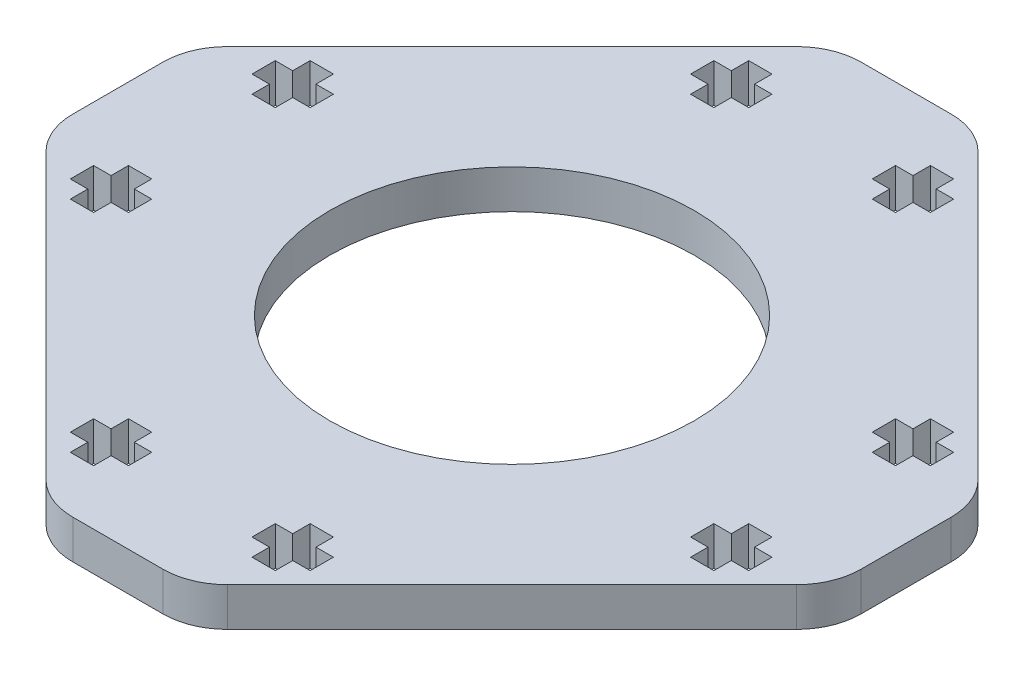
SolidWorks part; units mm, degrees
ref_plane "Front Plane" through (0, 0, 0) normal (0, 0, 1) x (1, 0, 0)
ref_plane "Top Plane" through (0, 0, 0) normal (0, 1, 0) x (1, 0, 0)
ref_plane "Right Plane" through (0, 0, 0) normal (1, 0, 0) x (0, 0, -1)
sketch "Sketch1" plane through (0, 0, 0) normal (0, 1, 0) x (1, 0, 0)
  line L0 (3.4914, 30.5) -> (-3.4914, 30.5)
  line L1 (-7.0269, 29.0355) -> (-29.0355, 7.0269)
  line L2 (-30.5, 3.4914) -> (-30.5, -3.4914)
  line L3 (-29.0355, -7.0269) -> (-7.0269, -29.0355)
  line L4 (-3.4914, -30.5) -> (3.4914, -30.5)
  line L5 (7.0269, -29.0355) -> (29.0355, -7.0269)
  line L7 (29.0355, 7.0269) -> (7.0269, 29.0355)
  line L13 (30.5, -3.4914) -> (30.5, 3.4914) construction
  line L14 (30.5, -3.4914) -> (30.5, 3.4914)
  arc A0 (7.0269, 29.0355) -> (3.4914, 30.5) centre (3.4914, 25.5) ccw
  arc A1 (-3.4914, 30.5) -> (-7.0269, 29.0355) centre (-3.4914, 25.5) ccw
  arc A2 (-29.0355, 7.0269) -> (-30.5, 3.4914) centre (-25.5, 3.4914) ccw
  arc A3 (-30.5, -3.4914) -> (-29.0355, -7.0269) centre (-25.5, -3.4914) ccw
  arc A4 (-7.0269, -29.0355) -> (-3.4914, -30.5) centre (-3.4914, -25.5) ccw
  arc A5 (3.4914, -30.5) -> (7.0269, -29.0355) centre (3.4914, -25.5) ccw
  circle A16 centre (0, 0) radius 14.1
  arc A17 (29.0355, -7.0269) -> (30.5, -3.4914) centre (25.5, -3.4914) ccw construction
  arc A18 (30.5, 3.4914) -> (29.0355, 7.0269) centre (25.5, 3.4914) ccw construction
  arc A19 (29.0355, -7.0269) -> (30.5, -3.4914) centre (25.5, -3.4914) ccw
  arc A20 (30.5, 3.4914) -> (29.0355, 7.0269) centre (25.5, 3.4914) ccw
  dimension "D1" = 28.2
  dimension "D2" = 31.1249
  dimension "D3" = 51
extrude "Boss-Extrude1" add sketch "Sketch1" along normal blind 3
sketch "Sketch2" plane through (0, 3, 0) normal (0, 1, 0) x (1, 0, 0)
  line L12 (-26.25, 7.9294) -> (-26.25, 6.1294)
  line L13 (-26.25, 6.1294) -> (-24.9, 6.1294)
  line L14 (-24.9, 6.1294) -> (-24.9, 4.7794)
  line L15 (-24.9, 4.7794) -> (-23.1, 4.7794)
  line L16 (-23.1, 4.7794) -> (-23.1, 6.1294)
  line L17 (-23.1, 6.1294) -> (-21.75, 6.1294)
  line L18 (-21.75, 6.1294) -> (-21.75, 7.9294)
  line L19 (-21.75, 7.9294) -> (-23.1, 7.9294)
  line L20 (-23.1, 7.9294) -> (-23.1, 9.2794)
  line L21 (-23.1, 9.2794) -> (-24.9, 9.2794)
  line L22 (-24.9, 9.2794) -> (-24.9, 7.9294)
  line L23 (-24.9, 7.9294) -> (-26.25, 7.9294)
  line L24 (-26.25, 7.9294) -> (-26.25, 6.1294)
  line L25 (-26.25, 6.1294) -> (-24.9, 6.1294)
  line L26 (-24.9, 6.1294) -> (-24.9, 4.7794)
  line L27 (-24.9, 4.7794) -> (-23.1, 4.7794)
  line L28 (-23.1, 4.7794) -> (-23.1, 6.1294)
  line L29 (-23.1, 6.1294) -> (-21.75, 6.1294)
  line L30 (-21.75, 6.1294) -> (-21.75, 7.9294)
  line L31 (-21.75, 7.9294) -> (-23.1, 7.9294)
  line L32 (-23.1, 7.9294) -> (-23.1, 9.2794)
  line L33 (-23.1, 9.2794) -> (-24.9, 9.2794)
  line L34 (-24.9, 9.2794) -> (-24.9, 7.9294)
  line L35 (-24.9, 7.9294) -> (-26.25, 7.9294)
  line L36 (-23.1, -4.7794) -> (-24.9, -4.7794)
  line L37 (-24.9, -4.7794) -> (-24.9, -6.1294)
  line L38 (-24.9, -6.1294) -> (-26.25, -6.1294)
  line L39 (-26.25, -6.1294) -> (-26.25, -7.9294)
  line L40 (-26.25, -7.9294) -> (-24.9, -7.9294)
  line L41 (-24.9, -7.9294) -> (-24.9, -9.2794)
  line L42 (-24.9, -9.2794) -> (-23.1, -9.2794)
  line L43 (-23.1, -9.2794) -> (-23.1, -7.9294)
  line L44 (-23.1, -7.9294) -> (-21.75, -7.9294)
  line L45 (-21.75, -7.9294) -> (-21.75, -6.1294)
  line L46 (-21.75, -6.1294) -> (-23.1, -6.1294)
  line L47 (-23.1, -6.1294) -> (-23.1, -4.7794)
  line L48 (-23.1, -4.7794) -> (-24.9, -4.7794)
  line L49 (-24.9, -4.7794) -> (-24.9, -6.1294)
  line L50 (-24.9, -6.1294) -> (-26.25, -6.1294)
  line L51 (-26.25, -6.1294) -> (-26.25, -7.9294)
  line L52 (-26.25, -7.9294) -> (-24.9, -7.9294)
  line L53 (-24.9, -7.9294) -> (-24.9, -9.2794)
  line L54 (-24.9, -9.2794) -> (-23.1, -9.2794)
  line L55 (-23.1, -9.2794) -> (-23.1, -7.9294)
  line L56 (-23.1, -7.9294) -> (-21.75, -7.9294)
  line L57 (-21.75, -7.9294) -> (-21.75, -6.1294)
  line L58 (-21.75, -6.1294) -> (-23.1, -6.1294)
  line L59 (-23.1, -6.1294) -> (-23.1, -4.7794)
  line L60 (7.9294, 23.1) -> (9.2794, 23.1)
  line L61 (9.2794, 23.1) -> (9.2794, 24.9)
  line L62 (9.2794, 24.9) -> (7.9294, 24.9)
  line L63 (7.9294, 24.9) -> (7.9294, 26.25)
  line L64 (7.9294, 26.25) -> (6.1294, 26.25)
  line L65 (6.1294, 26.25) -> (6.1294, 24.9)
  line L66 (6.1294, 24.9) -> (4.7794, 24.9)
  line L67 (4.7794, 24.9) -> (4.7794, 23.1)
  line L68 (4.7794, 23.1) -> (6.1294, 23.1)
  line L69 (6.1294, 23.1) -> (6.1294, 21.75)
  line L70 (6.1294, 21.75) -> (7.9294, 21.75)
  line L71 (7.9294, 21.75) -> (7.9294, 23.1)
  line L72 (7.9294, 23.1) -> (9.2794, 23.1)
  line L73 (9.2794, 23.1) -> (9.2794, 24.9)
  line L74 (9.2794, 24.9) -> (7.9294, 24.9)
  line L75 (7.9294, 24.9) -> (7.9294, 26.25)
  line L76 (7.9294, 26.25) -> (6.1294, 26.25)
  line L77 (6.1294, 26.25) -> (6.1294, 24.9)
  line L78 (6.1294, 24.9) -> (4.7794, 24.9)
  line L79 (4.7794, 24.9) -> (4.7794, 23.1)
  line L80 (4.7794, 23.1) -> (6.1294, 23.1)
  line L81 (6.1294, 23.1) -> (6.1294, 21.75)
  line L82 (6.1294, 21.75) -> (7.9294, 21.75)
  line L83 (7.9294, 21.75) -> (7.9294, 23.1)
  line L84 (26.25, -7.9294) -> (26.25, -6.1294)
  line L85 (26.25, -6.1294) -> (24.9, -6.1294)
  line L86 (24.9, -6.1294) -> (24.9, -4.7794)
  line L87 (24.9, -4.7794) -> (23.1, -4.7794)
  line L88 (23.1, -4.7794) -> (23.1, -6.1294)
  line L89 (23.1, -6.1294) -> (21.75, -6.1294)
  line L90 (21.75, -6.1294) -> (21.75, -7.9294)
  line L91 (21.75, -7.9294) -> (23.1, -7.9294)
  line L92 (23.1, -7.9294) -> (23.1, -9.2794)
  line L93 (23.1, -9.2794) -> (24.9, -9.2794)
  line L94 (24.9, -9.2794) -> (24.9, -7.9294)
  line L95 (24.9, -7.9294) -> (26.25, -7.9294)
  line L96 (26.25, -7.9294) -> (26.25, -6.1294)
  line L97 (26.25, -6.1294) -> (24.9, -6.1294)
  line L98 (24.9, -6.1294) -> (24.9, -4.7794)
  line L99 (24.9, -4.7794) -> (23.1, -4.7794)
  line L100 (23.1, -4.7794) -> (23.1, -6.1294)
  line L101 (23.1, -6.1294) -> (21.75, -6.1294)
  line L102 (21.75, -6.1294) -> (21.75, -7.9294)
  line L103 (21.75, -7.9294) -> (23.1, -7.9294)
  line L104 (23.1, -7.9294) -> (23.1, -9.2794)
  line L105 (23.1, -9.2794) -> (24.9, -9.2794)
  line L106 (24.9, -9.2794) -> (24.9, -7.9294)
  line L107 (24.9, -7.9294) -> (26.25, -7.9294)
  line L108 (-4.7794, 24.9) -> (-6.1294, 24.9)
  line L109 (-6.1294, 24.9) -> (-6.1294, 26.25)
  line L110 (-6.1294, 26.25) -> (-7.9294, 26.25)
  line L111 (-7.9294, 26.25) -> (-7.9294, 24.9)
  line L112 (-7.9294, 24.9) -> (-9.2794, 24.9)
  line L113 (-9.2794, 24.9) -> (-9.2794, 23.1)
  line L114 (-9.2794, 23.1) -> (-7.9294, 23.1)
  line L115 (-7.9294, 23.1) -> (-7.9294, 21.75)
  line L116 (-7.9294, 21.75) -> (-6.1294, 21.75)
  line L117 (-6.1294, 21.75) -> (-6.1294, 23.1)
  line L118 (-6.1294, 23.1) -> (-4.7794, 23.1)
  line L119 (-4.7794, 23.1) -> (-4.7794, 24.9)
  line L120 (-4.7794, 24.9) -> (-6.1294, 24.9)
  line L121 (-6.1294, 24.9) -> (-6.1294, 26.25)
  line L122 (-6.1294, 26.25) -> (-7.9294, 26.25)
  line L123 (-7.9294, 26.25) -> (-7.9294, 24.9)
  line L124 (-7.9294, 24.9) -> (-9.2794, 24.9)
  line L125 (-9.2794, 24.9) -> (-9.2794, 23.1)
  line L126 (-9.2794, 23.1) -> (-7.9294, 23.1)
  line L127 (-7.9294, 23.1) -> (-7.9294, 21.75)
  line L128 (-7.9294, 21.75) -> (-6.1294, 21.75)
  line L129 (-6.1294, 21.75) -> (-6.1294, 23.1)
  line L130 (-6.1294, 23.1) -> (-4.7794, 23.1)
  line L131 (-4.7794, 23.1) -> (-4.7794, 24.9)
  line L132 (26.25, 7.9294) -> (24.9, 7.9294)
  line L133 (26.25, 6.1294) -> (26.25, 7.9294)
  line L134 (24.9, 6.1294) -> (26.25, 6.1294)
  line L135 (24.9, 4.7794) -> (24.9, 6.1294)
  line L136 (23.1, 4.7794) -> (24.9, 4.7794)
  line L137 (23.1, 6.1294) -> (23.1, 4.7794)
  line L138 (21.75, 6.1294) -> (23.1, 6.1294)
  line L139 (21.75, 7.9294) -> (21.75, 6.1294)
  line L140 (23.1, 7.9294) -> (21.75, 7.9294)
  line L141 (23.1, 9.2794) -> (23.1, 7.9294)
  line L142 (24.9, 9.2794) -> (23.1, 9.2794)
  line L143 (24.9, 7.9294) -> (24.9, 9.2794)
  line L144 (26.25, 7.9294) -> (24.9, 7.9294)
  line L145 (26.25, 6.1294) -> (26.25, 7.9294)
  line L146 (24.9, 6.1294) -> (26.25, 6.1294)
  line L147 (24.9, 4.7794) -> (24.9, 6.1294)
  line L148 (23.1, 4.7794) -> (24.9, 4.7794)
  line L149 (23.1, 6.1294) -> (23.1, 4.7794)
  line L150 (21.75, 6.1294) -> (23.1, 6.1294)
  line L151 (21.75, 7.9294) -> (21.75, 6.1294)
  line L152 (23.1, 7.9294) -> (21.75, 7.9294)
  line L153 (23.1, 9.2794) -> (23.1, 7.9294)
  line L154 (24.9, 9.2794) -> (23.1, 9.2794)
  line L155 (24.9, 7.9294) -> (24.9, 9.2794)
  line L156 (-6.1294, -26.25) -> (-6.1294, -24.9)
  line L157 (-6.1294, -24.9) -> (-4.7794, -24.9)
  line L158 (-4.7794, -24.9) -> (-4.7794, -23.1)
  line L159 (-4.7794, -23.1) -> (-6.1294, -23.1)
  line L160 (-6.1294, -23.1) -> (-6.1294, -21.75)
  line L161 (-6.1294, -21.75) -> (-7.9294, -21.75)
  line L162 (-7.9294, -21.75) -> (-7.9294, -23.1)
  line L163 (-7.9294, -23.1) -> (-9.2794, -23.1)
  line L164 (-9.2794, -23.1) -> (-9.2794, -24.9)
  line L165 (-9.2794, -24.9) -> (-7.9294, -24.9)
  line L166 (-7.9294, -24.9) -> (-7.9294, -26.25)
  line L167 (-7.9294, -26.25) -> (-6.1294, -26.25)
  line L168 (-6.1294, -26.25) -> (-6.1294, -24.9)
  line L169 (-6.1294, -24.9) -> (-4.7794, -24.9)
  line L170 (-4.7794, -24.9) -> (-4.7794, -23.1)
  line L171 (-4.7794, -23.1) -> (-6.1294, -23.1)
  line L172 (-6.1294, -23.1) -> (-6.1294, -21.75)
  line L173 (-6.1294, -21.75) -> (-7.9294, -21.75)
  line L174 (-7.9294, -21.75) -> (-7.9294, -23.1)
  line L175 (-7.9294, -23.1) -> (-9.2794, -23.1)
  line L176 (-9.2794, -23.1) -> (-9.2794, -24.9)
  line L177 (-9.2794, -24.9) -> (-7.9294, -24.9)
  line L178 (-7.9294, -24.9) -> (-7.9294, -26.25)
  line L179 (-7.9294, -26.25) -> (-6.1294, -26.25)
  line L180 (7.9294, -26.25) -> (7.9294, -24.9)
  line L181 (7.9294, -24.9) -> (9.2794, -24.9)
  line L182 (9.2794, -24.9) -> (9.2794, -23.1)
  line L183 (9.2794, -23.1) -> (7.9294, -23.1)
  line L184 (7.9294, -23.1) -> (7.9294, -21.75)
  line L185 (7.9294, -21.75) -> (6.1294, -21.75)
  line L186 (6.1294, -21.75) -> (6.1294, -23.1)
  line L187 (6.1294, -23.1) -> (4.7794, -23.1)
  line L188 (4.7794, -23.1) -> (4.7794, -24.9)
  line L189 (4.7794, -24.9) -> (6.1294, -24.9)
  line L190 (6.1294, -24.9) -> (6.1294, -26.25)
  line L191 (6.1294, -26.25) -> (7.9294, -26.25)
  line L192 (7.9294, -26.25) -> (7.9294, -24.9)
  line L193 (7.9294, -24.9) -> (9.2794, -24.9)
  line L194 (9.2794, -24.9) -> (9.2794, -23.1)
  line L195 (9.2794, -23.1) -> (7.9294, -23.1)
  line L196 (7.9294, -23.1) -> (7.9294, -21.75)
  line L197 (7.9294, -21.75) -> (6.1294, -21.75)
  line L198 (6.1294, -21.75) -> (6.1294, -23.1)
  line L199 (6.1294, -23.1) -> (4.7794, -23.1)
  line L200 (4.7794, -23.1) -> (4.7794, -24.9)
  line L201 (4.7794, -24.9) -> (6.1294, -24.9)
  line L202 (6.1294, -24.9) -> (6.1294, -26.25)
  line L203 (6.1294, -26.25) -> (7.9294, -26.25)
  dimension "D1" = 0
  dimension "D2" = 0
  dimension "D3" = 0
  dimension "D4" = 0
  dimension "D5" = 0
  dimension "D6" = 0
  dimension "D7" = 0
  dimension "D8" = 0
extrude "Cut-Extrude1" cut sketch "Sketch2" against normal through all
sketch "Sketch3" plane through (0, 3, 0) normal (0, 1, 0) x (1, 0, 0)
  line L8 (3.4914, 30.5) -> (-3.4914, 30.5)
  line L9 (-7.0269, 29.0355) -> (-29.0355, 7.0269)
  line L10 (-30.5, 3.4914) -> (-30.5, -3.4914)
  line L11 (-29.0355, -7.0269) -> (-7.0269, -29.0355)
  line L12 (-3.4914, -30.5) -> (3.4914, -30.5)
  line L13 (7.0269, -29.0355) -> (29.0355, -7.0269)
  line L14 (30.5, -3.4914) -> (30.5, 3.4914)
  line L15 (29.0355, 7.0269) -> (7.0269, 29.0355)
  line L16 (3.4914, 30.5) -> (-3.4914, 30.5)
  line L17 (-7.0269, 29.0355) -> (-29.0355, 7.0269)
  line L18 (-30.5, 3.4914) -> (-30.5, -3.4914)
  line L19 (-29.0355, -7.0269) -> (-7.0269, -29.0355)
  line L20 (-3.4914, -30.5) -> (3.4914, -30.5)
  line L21 (7.0269, -29.0355) -> (29.0355, -7.0269)
  line L22 (30.5, -3.4914) -> (30.5, 3.4914)
  line L23 (29.0355, 7.0269) -> (7.0269, 29.0355)
  line L28 (-24.9, 7.9294) -> (-26.25, 7.9294)
  line L29 (-24.9, 9.2794) -> (-24.9, 7.9294)
  line L30 (-23.1, 9.2794) -> (-24.9, 9.2794)
  line L31 (-23.1, 7.9294) -> (-23.1, 9.2794)
  line L32 (-21.75, 7.9294) -> (-23.1, 7.9294)
  line L33 (-21.75, 6.1294) -> (-21.75, 7.9294)
  line L34 (-23.1, 6.1294) -> (-21.75, 6.1294)
  line L35 (-23.1, 4.7794) -> (-23.1, 6.1294)
  line L36 (-24.9, 4.7794) -> (-23.1, 4.7794)
  line L37 (-24.9, 6.1294) -> (-24.9, 4.7794)
  line L38 (-26.25, 6.1294) -> (-24.9, 6.1294)
  line L39 (-26.25, 7.9294) -> (-26.25, 6.1294)
  line L40 (-24.9, 7.9294) -> (-26.25, 7.9294)
  line L41 (-24.9, 9.2794) -> (-24.9, 7.9294)
  line L42 (-23.1, 9.2794) -> (-24.9, 9.2794)
  line L43 (-23.1, 7.9294) -> (-23.1, 9.2794)
  line L44 (-21.75, 7.9294) -> (-23.1, 7.9294)
  line L45 (-21.75, 6.1294) -> (-21.75, 7.9294)
  line L46 (-23.1, 6.1294) -> (-21.75, 6.1294)
  line L47 (-23.1, 4.7794) -> (-23.1, 6.1294)
  line L48 (-24.9, 4.7794) -> (-23.1, 4.7794)
  line L49 (-24.9, 6.1294) -> (-24.9, 4.7794)
  line L50 (-26.25, 6.1294) -> (-24.9, 6.1294)
  line L51 (-26.25, 7.9294) -> (-26.25, 6.1294)
  line L52 (24.9, 7.9294) -> (24.9, 9.2794)
  line L53 (26.25, 7.9294) -> (24.9, 7.9294)
  line L54 (26.25, 6.1294) -> (26.25, 7.9294)
  line L55 (24.9, 6.1294) -> (26.25, 6.1294)
  line L56 (24.9, 4.7794) -> (24.9, 6.1294)
  line L57 (23.1, 4.7794) -> (24.9, 4.7794)
  line L58 (23.1, 6.1294) -> (23.1, 4.7794)
  line L59 (21.75, 6.1294) -> (23.1, 6.1294)
  line L60 (21.75, 7.9294) -> (21.75, 6.1294)
  line L61 (23.1, 7.9294) -> (21.75, 7.9294)
  line L62 (23.1, 9.2794) -> (23.1, 7.9294)
  line L63 (24.9, 9.2794) -> (23.1, 9.2794)
  line L64 (24.9, 7.9294) -> (24.9, 9.2794)
  line L65 (26.25, 7.9294) -> (24.9, 7.9294)
  line L66 (26.25, 6.1294) -> (26.25, 7.9294)
  line L67 (24.9, 6.1294) -> (26.25, 6.1294)
  line L68 (24.9, 4.7794) -> (24.9, 6.1294)
  line L69 (23.1, 4.7794) -> (24.9, 4.7794)
  line L70 (23.1, 6.1294) -> (23.1, 4.7794)
  line L71 (21.75, 6.1294) -> (23.1, 6.1294)
  line L72 (21.75, 7.9294) -> (21.75, 6.1294)
  line L73 (23.1, 7.9294) -> (21.75, 7.9294)
  line L74 (23.1, 9.2794) -> (23.1, 7.9294)
  line L75 (24.9, 9.2794) -> (23.1, 9.2794)
  line L76 (-7.9294, -26.25) -> (-6.1294, -26.25)
  line L77 (-7.9294, -24.9) -> (-7.9294, -26.25)
  line L78 (-9.2794, -24.9) -> (-7.9294, -24.9)
  line L79 (-9.2794, -23.1) -> (-9.2794, -24.9)
  line L80 (-7.9294, -23.1) -> (-9.2794, -23.1)
  line L81 (-7.9294, -21.75) -> (-7.9294, -23.1)
  line L82 (-6.1294, -21.75) -> (-7.9294, -21.75)
  line L83 (-6.1294, -23.1) -> (-6.1294, -21.75)
  line L84 (-4.7794, -23.1) -> (-6.1294, -23.1)
  line L85 (-4.7794, -24.9) -> (-4.7794, -23.1)
  line L86 (-6.1294, -24.9) -> (-4.7794, -24.9)
  line L87 (-6.1294, -26.25) -> (-6.1294, -24.9)
  line L88 (-7.9294, -26.25) -> (-6.1294, -26.25)
  line L89 (-7.9294, -24.9) -> (-7.9294, -26.25)
  line L90 (-9.2794, -24.9) -> (-7.9294, -24.9)
  line L91 (-9.2794, -23.1) -> (-9.2794, -24.9)
  line L92 (-7.9294, -23.1) -> (-9.2794, -23.1)
  line L93 (-7.9294, -21.75) -> (-7.9294, -23.1)
  line L94 (-6.1294, -21.75) -> (-7.9294, -21.75)
  line L95 (-6.1294, -23.1) -> (-6.1294, -21.75)
  line L96 (-4.7794, -23.1) -> (-6.1294, -23.1)
  line L97 (-4.7794, -24.9) -> (-4.7794, -23.1)
  line L98 (-6.1294, -24.9) -> (-4.7794, -24.9)
  line L99 (-6.1294, -26.25) -> (-6.1294, -24.9)
  line L100 (7.9294, -24.9) -> (9.2794, -24.9)
  line L101 (7.9294, -26.25) -> (7.9294, -24.9)
  line L102 (6.1294, -26.25) -> (7.9294, -26.25)
  line L103 (6.1294, -24.9) -> (6.1294, -26.25)
  line L104 (4.7794, -24.9) -> (6.1294, -24.9)
  line L105 (4.7794, -23.1) -> (4.7794, -24.9)
  line L106 (6.1294, -23.1) -> (4.7794, -23.1)
  line L107 (6.1294, -21.75) -> (6.1294, -23.1)
  line L108 (7.9294, -21.75) -> (6.1294, -21.75)
  line L109 (7.9294, -23.1) -> (7.9294, -21.75)
  line L110 (9.2794, -23.1) -> (7.9294, -23.1)
  line L111 (9.2794, -24.9) -> (9.2794, -23.1)
  line L112 (7.9294, -24.9) -> (9.2794, -24.9)
  line L113 (7.9294, -26.25) -> (7.9294, -24.9)
  line L114 (6.1294, -26.25) -> (7.9294, -26.25)
  line L115 (6.1294, -24.9) -> (6.1294, -26.25)
  line L116 (4.7794, -24.9) -> (6.1294, -24.9)
  line L117 (4.7794, -23.1) -> (4.7794, -24.9)
  line L118 (6.1294, -23.1) -> (4.7794, -23.1)
  line L119 (6.1294, -21.75) -> (6.1294, -23.1)
  line L120 (7.9294, -21.75) -> (6.1294, -21.75)
  line L121 (7.9294, -23.1) -> (7.9294, -21.75)
  line L122 (9.2794, -23.1) -> (7.9294, -23.1)
  line L123 (9.2794, -24.9) -> (9.2794, -23.1)
  line L124 (-24.9, -4.7794) -> (-24.9, -6.1294)
  line L125 (-23.1, -4.7794) -> (-24.9, -4.7794)
  line L126 (-23.1, -6.1294) -> (-23.1, -4.7794)
  line L127 (-21.75, -6.1294) -> (-23.1, -6.1294)
  line L128 (-21.75, -7.9294) -> (-21.75, -6.1294)
  line L129 (-23.1, -7.9294) -> (-21.75, -7.9294)
  line L130 (-23.1, -9.2794) -> (-23.1, -7.9294)
  line L131 (-24.9, -9.2794) -> (-23.1, -9.2794)
  line L132 (-24.9, -7.9294) -> (-24.9, -9.2794)
  line L133 (-26.25, -7.9294) -> (-24.9, -7.9294)
  line L134 (-26.25, -6.1294) -> (-26.25, -7.9294)
  line L135 (-24.9, -6.1294) -> (-26.25, -6.1294)
  line L136 (-24.9, -4.7794) -> (-24.9, -6.1294)
  line L137 (-23.1, -4.7794) -> (-24.9, -4.7794)
  line L138 (-23.1, -6.1294) -> (-23.1, -4.7794)
  line L139 (-21.75, -6.1294) -> (-23.1, -6.1294)
  line L140 (-21.75, -7.9294) -> (-21.75, -6.1294)
  line L141 (-23.1, -7.9294) -> (-21.75, -7.9294)
  line L142 (-23.1, -9.2794) -> (-23.1, -7.9294)
  line L143 (-24.9, -9.2794) -> (-23.1, -9.2794)
  line L144 (-24.9, -7.9294) -> (-24.9, -9.2794)
  line L145 (-26.25, -7.9294) -> (-24.9, -7.9294)
  line L146 (-26.25, -6.1294) -> (-26.25, -7.9294)
  line L147 (-24.9, -6.1294) -> (-26.25, -6.1294)
  line L148 (7.9294, 21.75) -> (7.9294, 23.1)
  line L149 (6.1294, 21.75) -> (7.9294, 21.75)
  line L150 (6.1294, 23.1) -> (6.1294, 21.75)
  line L151 (4.7794, 23.1) -> (6.1294, 23.1)
  line L152 (4.7794, 24.9) -> (4.7794, 23.1)
  line L153 (6.1294, 24.9) -> (4.7794, 24.9)
  line L154 (6.1294, 26.25) -> (6.1294, 24.9)
  line L155 (7.9294, 26.25) -> (6.1294, 26.25)
  line L156 (7.9294, 24.9) -> (7.9294, 26.25)
  line L157 (9.2794, 24.9) -> (7.9294, 24.9)
  line L158 (9.2794, 23.1) -> (9.2794, 24.9)
  line L159 (7.9294, 23.1) -> (9.2794, 23.1)
  line L160 (7.9294, 21.75) -> (7.9294, 23.1)
  line L161 (6.1294, 21.75) -> (7.9294, 21.75)
  line L162 (6.1294, 23.1) -> (6.1294, 21.75)
  line L163 (4.7794, 23.1) -> (6.1294, 23.1)
  line L164 (4.7794, 24.9) -> (4.7794, 23.1)
  line L165 (6.1294, 24.9) -> (4.7794, 24.9)
  line L166 (6.1294, 26.25) -> (6.1294, 24.9)
  line L167 (7.9294, 26.25) -> (6.1294, 26.25)
  line L168 (7.9294, 24.9) -> (7.9294, 26.25)
  line L169 (9.2794, 24.9) -> (7.9294, 24.9)
  line L170 (9.2794, 23.1) -> (9.2794, 24.9)
  line L171 (7.9294, 23.1) -> (9.2794, 23.1)
  line L172 (24.9, -7.9294) -> (26.25, -7.9294)
  line L173 (24.9, -9.2794) -> (24.9, -7.9294)
  line L174 (23.1, -9.2794) -> (24.9, -9.2794)
  line L175 (23.1, -7.9294) -> (23.1, -9.2794)
  line L176 (21.75, -7.9294) -> (23.1, -7.9294)
  line L177 (21.75, -6.1294) -> (21.75, -7.9294)
  line L178 (23.1, -6.1294) -> (21.75, -6.1294)
  line L179 (23.1, -4.7794) -> (23.1, -6.1294)
  line L180 (24.9, -4.7794) -> (23.1, -4.7794)
  line L181 (24.9, -6.1294) -> (24.9, -4.7794)
  line L182 (26.25, -6.1294) -> (24.9, -6.1294)
  line L183 (26.25, -7.9294) -> (26.25, -6.1294)
  line L184 (24.9, -7.9294) -> (26.25, -7.9294)
  line L185 (24.9, -9.2794) -> (24.9, -7.9294)
  line L186 (23.1, -9.2794) -> (24.9, -9.2794)
  line L187 (23.1, -7.9294) -> (23.1, -9.2794)
  line L188 (21.75, -7.9294) -> (23.1, -7.9294)
  line L189 (21.75, -6.1294) -> (21.75, -7.9294)
  line L190 (23.1, -6.1294) -> (21.75, -6.1294)
  line L191 (23.1, -4.7794) -> (23.1, -6.1294)
  line L192 (24.9, -4.7794) -> (23.1, -4.7794)
  line L193 (24.9, -6.1294) -> (24.9, -4.7794)
  line L194 (26.25, -6.1294) -> (24.9, -6.1294)
  line L195 (26.25, -7.9294) -> (26.25, -6.1294)
  line L196 (-6.1294, 24.9) -> (-6.1294, 26.25)
  line L197 (-4.7794, 24.9) -> (-6.1294, 24.9)
  line L198 (-4.7794, 23.1) -> (-4.7794, 24.9)
  line L199 (-6.1294, 23.1) -> (-4.7794, 23.1)
  line L200 (-6.1294, 21.75) -> (-6.1294, 23.1)
  line L201 (-7.9294, 21.75) -> (-6.1294, 21.75)
  line L202 (-7.9294, 23.1) -> (-7.9294, 21.75)
  line L203 (-9.2794, 23.1) -> (-7.9294, 23.1)
  line L204 (-9.2794, 24.9) -> (-9.2794, 23.1)
  line L205 (-7.9294, 24.9) -> (-9.2794, 24.9)
  line L206 (-7.9294, 26.25) -> (-7.9294, 24.9)
  line L207 (-6.1294, 26.25) -> (-7.9294, 26.25)
  line L208 (-6.1294, 24.9) -> (-6.1294, 26.25)
  line L209 (-4.7794, 24.9) -> (-6.1294, 24.9)
  line L210 (-4.7794, 23.1) -> (-4.7794, 24.9)
  line L211 (-6.1294, 23.1) -> (-4.7794, 23.1)
  line L212 (-6.1294, 21.75) -> (-6.1294, 23.1)
  line L213 (-7.9294, 21.75) -> (-6.1294, 21.75)
  line L214 (-7.9294, 23.1) -> (-7.9294, 21.75)
  line L215 (-9.2794, 23.1) -> (-7.9294, 23.1)
  line L216 (-9.2794, 24.9) -> (-9.2794, 23.1)
  line L217 (-7.9294, 24.9) -> (-9.2794, 24.9)
  line L218 (-7.9294, 26.25) -> (-7.9294, 24.9)
  line L219 (-6.1294, 26.25) -> (-7.9294, 26.25)
  circle A1 centre (0, 0) radius 14.1
  circle A2 centre (0, 0) radius 14.1
  arc A8 (7.0269, 29.0355) -> (3.4914, 30.5) centre (3.4914, 25.5) ccw
  arc A9 (-3.4914, 30.5) -> (-7.0269, 29.0355) centre (-3.4914, 25.5) ccw
  arc A10 (-29.0355, 7.0269) -> (-30.5, 3.4914) centre (-25.5, 3.4914) ccw
  arc A11 (-30.5, -3.4914) -> (-29.0355, -7.0269) centre (-25.5, -3.4914) ccw
  arc A12 (-7.0269, -29.0355) -> (-3.4914, -30.5) centre (-3.4914, -25.5) ccw
  arc A13 (3.4914, -30.5) -> (7.0269, -29.0355) centre (3.4914, -25.5) ccw
  arc A14 (29.0355, -7.0269) -> (30.5, -3.4914) centre (25.5, -3.4914) ccw
  arc A15 (30.5, 3.4914) -> (29.0355, 7.0269) centre (25.5, 3.4914) ccw
  arc A16 (7.0269, 29.0355) -> (3.4914, 30.5) centre (3.4914, 25.5) ccw
  arc A17 (-3.4914, 30.5) -> (-7.0269, 29.0355) centre (-3.4914, 25.5) ccw
  arc A18 (-29.0355, 7.0269) -> (-30.5, 3.4914) centre (-25.5, 3.4914) ccw
  arc A19 (-30.5, -3.4914) -> (-29.0355, -7.0269) centre (-25.5, -3.4914) ccw
  arc A20 (-7.0269, -29.0355) -> (-3.4914, -30.5) centre (-3.4914, -25.5) ccw
  arc A21 (3.4914, -30.5) -> (7.0269, -29.0355) centre (3.4914, -25.5) ccw
  arc A22 (29.0355, -7.0269) -> (30.5, -3.4914) centre (25.5, -3.4914) ccw
  arc A23 (30.5, 3.4914) -> (29.0355, 7.0269) centre (25.5, 3.4914) ccw
  dimension "D1" = 0
  dimension "D2" = 0
  dimension "D3" = 0
  dimension "D4" = 0
  dimension "D5" = 0
  dimension "D6" = 0
  dimension "D7" = 0
  dimension "D8" = 0
  dimension "D9" = 0
  dimension "D10" = 0
